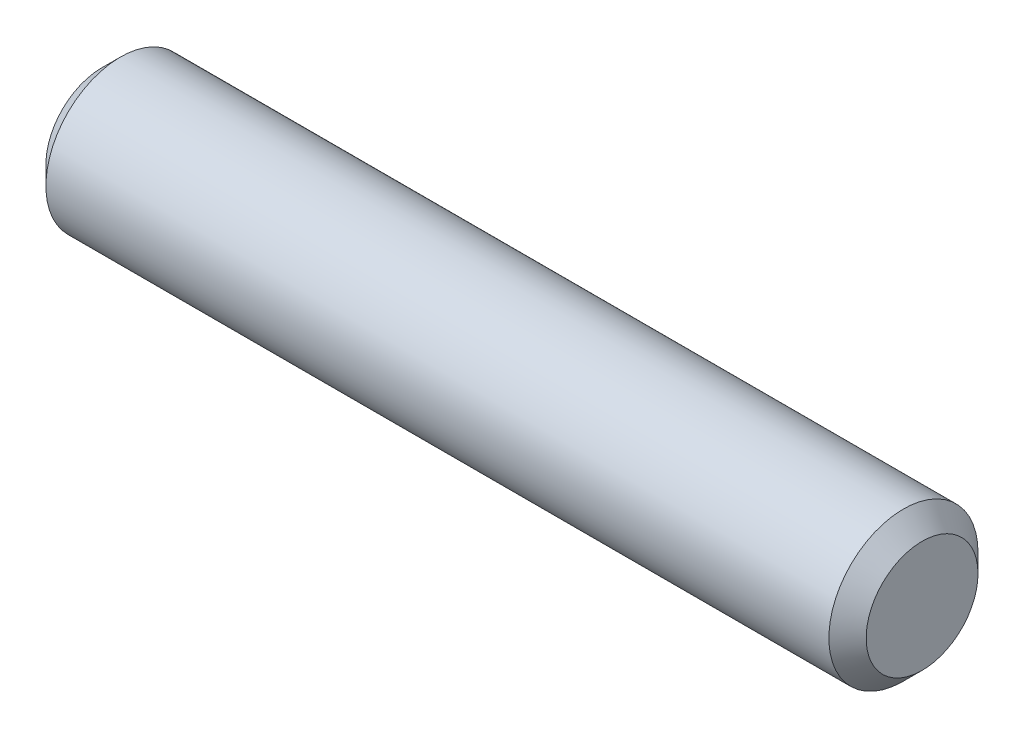
SolidWorks part; units mm, degrees
ref_plane "Front Plane" through (0, 0, 0) normal (0, 0, 1) x (1, 0, 0)
ref_plane "Top Plane" through (0, 0, 0) normal (0, 1, 0) x (1, 0, 0)
ref_plane "Right Plane" through (0, 0, 0) normal (1, 0, 0) x (0, 0, -1)
sketch "Sketch1" plane through (0, 0, 0) normal (1, 0, 0) x (0, 0, -1)
  circle A0 centre (0, 0) radius 2
extrude "Boss-Extrude1" add sketch "Sketch1" along normal blind 22
chamfer "Chamfer1" distance 0.5 angle 45 2 edges at (0, 0, -2) (22, 0, -2)
